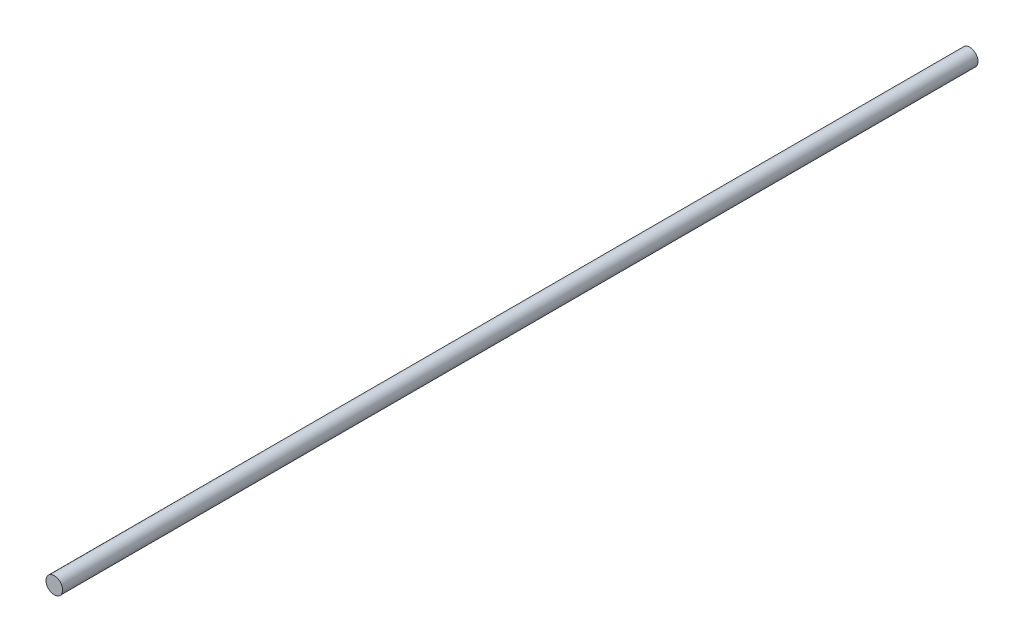
SolidWorks part; units mm, degrees
ref_plane "Ön Düzlem" through (0, 0, 0) normal (0, 0, 1) x (1, 0, 0)
ref_plane "Üst Düzlem" through (0, 0, 0) normal (0, 1, 0) x (1, 0, 0)
ref_plane "Sağ Düzlem" through (0, 0, 0) normal (1, 0, 0) x (0, 0, -1)
sketch "Çizim1" plane through (0, 0, 0) normal (0, 0, 1) x (1, 0, 0)
  circle A0 centre (0, 0) radius 6
  dimension "D1" = 12
extrude "Yükseklik-Ekstrüzyon1" add sketch "Çizim1" along normal blind 662
